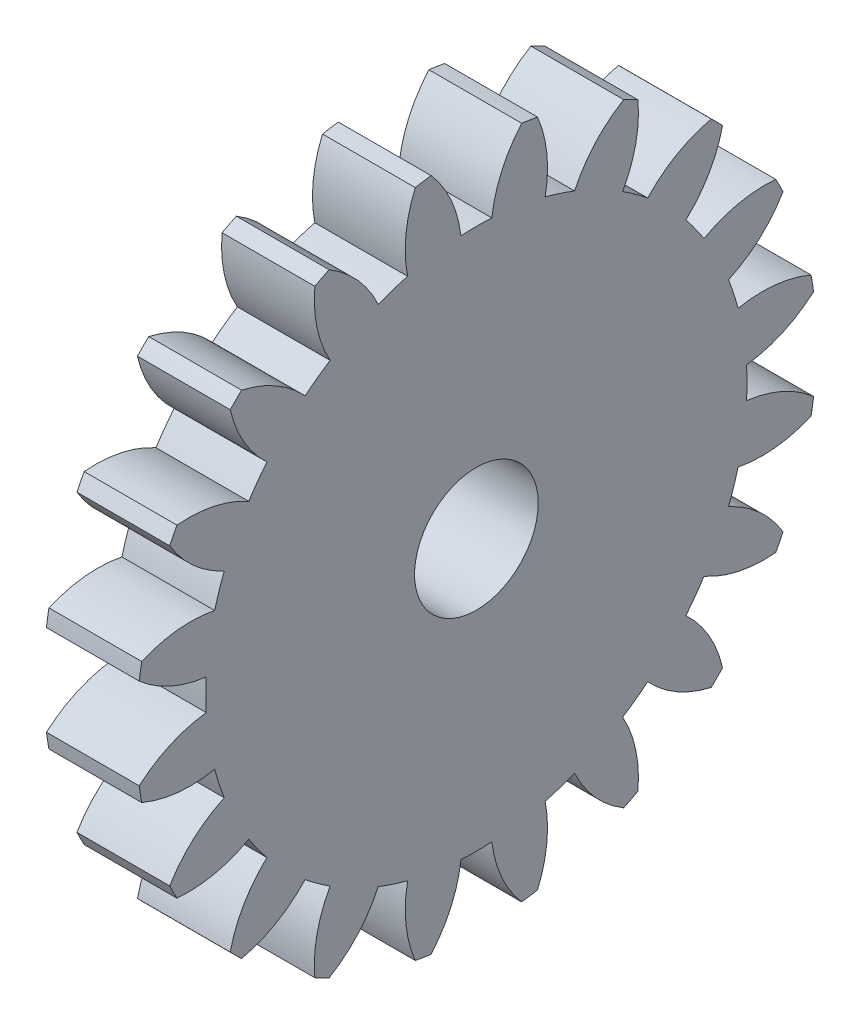
SolidWorks part; units mm, degrees
ref_plane "Plane1" through (0, 0, 0) normal (0, 0, 1) x (1, 0, 0)
ref_plane "Plane2" through (0, 0, 0) normal (0, 1, 0) x (1, 0, 0)
ref_plane "Plane3" through (0, 0, 0) normal (1, 0, 0) x (0, 0, -1)
sketch "HoldingSke" plane through (0, 0, 0) normal (0, 1, 0) x (1, 0, 0)
  line L0 (0, 0) -> (0.9397, -0.342)
  line L1 (-15, 0) -> (100, 0) construction
  line L2 (0, 0) -> (-2.1039, 2.3779)
  line L3 (0, 0) -> (-11.863, 4.5341)
  line L4 (0, 0) -> (8.1152, 2.9537)
  line L5 (0, 0) -> (-46.8476, -17.4728)
  line L6 (0, 0) -> (-2.4869, -1.6779)
  line L7 (-2.1039, 2.3779) -> (8.6586, 51.2059)
  line L8 (-76.2, 54.61) -> (-75.7, 54.61)
  line L9 (-71.009, 38.7566) -> (-53.1078, 45.2721)
  line L10 (-76.2, 71.12) -> (104.1128, 71.12)
  line L11 (0, 0) -> (-3, 0)
  line L12 (-76.2, 101.6) -> (-76.162, 101.6)
  line L13 (24.9733, 27.94) -> (52.9518, 28.4284)
  line L14 (24.9733, 27.94) -> (24.9743, 27.94)
  line L15 (24.9733, 27.94) -> (100.4006, 29.5858)
  line L16 (-63.627, -1) -> (-12.827, -1)
  circle A0 centre (0, 0) radius 1.5
  circle A1 centre (0, 0) radius 8.749
  circle A2 centre (0, 0) radius 37.5
  circle A3 centre (0, 0) radius 1.5
  dimension "MHD" = 17.498
  dimension "Hub_dia" = 75
  dimension "Bore" = 3
  dimension "MBD" = 3
  dimension "Num_teeth" = 20
  dimension "Pitch" = 1
  dimension "Overall_len" = 50
  dimension "Show_teeth" = 20
  dimension "Thickness" = 3
  dimension "OAL" = 50.0001
  dimension "T_dim" = 0.5
  dimension "Ap" = 20
  dimension "H" = 19.05
  dimension "Pitch_radius" = 180.3128
  dimension "Width" = 3
  dimension "Backlash" = 0.038
  dimension "Addendum_fac" = 1
  dimension "Dedendum_fac" = 1.25
  dimension "Clearance_fac" = 0.25
  dimension "Dedendum_add" = 0.001
  dimension "Module" = 1
sketch "BasProSke" plane through (0, 0, 0) normal (0, 1, 0) x (1, 0, 0)
  line L0 (-10, 0) -> (60, 0) construction
  line L1 (0, 0) -> (0, 11)
  line L2 (0, 0) -> (3, 0)
  line L3 (3, 0) -> (3, 11)
  line L4 (3, 11) -> (0, 11)
  dimension "Thickness" = 3
  dimension "Diameter" = 22
revolve "Base-Revolve" add sketch "BasProSke" angle 360 about L0
sketch "TooCutSke" plane through (0, 0, 0) normal (1, 0, 0) x (0, 0, -1)
  line L1 (0, 0) -> (0, 107) construction
  line L2 (0, 0) -> (-0.8511, 9.9637) construction
  line L3 (0, 0) -> (-3.1206, 19.7028) construction
  line L4 (-0.8511, 9.9637) -> (-1.5603, 9.8514) construction
  arc A0 (0.4999, 8.7347) -> (-0.4999, 8.7347) centre (0, 0) ccw
  arc A1 (1.4852, 10.9249) -> (-1.4852, 10.9249) centre (0, 0) ccw
  circle A2 centre (0, 0) radius 10 construction
  circle A3 centre (0, 0) radius 9.3969 construction
  arc A4 (-0.4999, 8.7347) -> (-1.4852, 10.9249) centre (-4.4722, 8.2645) ccw
  arc A5 (1.4852, 10.9249) -> (0.4999, 8.7347) centre (4.4722, 8.2645) ccw
  dimension "Root_dia" = 17.498
  dimension "Overcut_dia" = 22.0508
  dimension "Pitch_dia" = 20
  dimension "Base_dia" = 18.7939
  dimension "Flank_rad" = 4
  dimension "Half_ang" = 9
  dimension "Half_CT" = 0.7181
extrude "ToothCut" cut sketch "TooCutSke" along normal through all
fillet "Breaks" [suppressed] radius 0.02
fillet "RootFillets" [suppressed] radius 0.251
pattern_circular "TeethCuts" count 20 every 18 about axis through (-10, 0, 0) along (1, 0, 0) of "ToothCut", "RootFillets", "Breaks"
sketch "HubNeaOneSke" plane through (0, 0, 0) normal (-1, 0, 0) x (0, 0, 1)
  circle A0 centre (0, 0) radius 8.749
  dimension "Diameter" = 17.498
extrude "HubNearOne" [suppressed] add sketch "HubNeaOneSke" along normal blind 47.0001
sketch "HubNeaBotSke" plane through (0, 0, 0) normal (-1, 0, 0) x (0, 0, 1)
  circle A0 centre (0, 0) radius 8.749
  dimension "Diameter" = 17.498
extrude "HubNearBoth" [suppressed] add sketch "HubNeaBotSke" along normal blind 23.5
ref_plane "FarPln" through (3, 0, 0) normal (1, 0, 0) x (0, 0, -1)
sketch "HubFarSke" plane through (3, 0, 0) normal (1, 0, 0) x (0, 0, -1)
  circle A0 centre (0, 0) radius 8.749
  dimension "Diameter" = 17.498
extrude "HubFar" [suppressed] add sketch "HubFarSke" along normal blind 23.5
sketch "BorSke" plane through (0, 0, 0) normal (1, 0, 0) x (0, 0, -1)
  circle A0 centre (0, 0) radius 1.5
  dimension "Diameter" = 3
extrude "Bore" cut sketch "BorSke" along normal mid plane 100.0001
sketch "KeySke" plane through (0, 0, 0) normal (1, 0, 0) x (0, 0, -1)
  line L0 (-0.6, 0) -> (-0.6, 2)
  line L1 (-0.6, 2) -> (0.6, 2)
  line L2 (0.6, 2) -> (0.6, 0)
  line L3 (0, 0) -> (0, 34) construction
  line L4 (-0.6, 0) -> (0.6, 0)
  dimension "Offset" = 2
  dimension "Width" = 1.2
extrude "Keyway" [suppressed] cut sketch "KeySke" along normal mid plane 100.0001
pattern_circular "Keyway2" [suppressed] count 2 every 90 about axis through (-10, 0, 0) along (1, 0, 0)
sketch "Sketch1" plane through (3, 0, 0) normal (1, 0, 0) x (0, 0, -1)
  circle A0 centre (0, 0) radius 2
  dimension "D1" = 4
extrude "Cut-Extrude1" cut sketch "Sketch1" against normal through all
equation "' \"Module@HoldingSke\" = 6.35"
equation "' \"Num_teeth@HoldingSke\" = 12"
equation "' \"Ap@HoldingSke\" =  20"
equation "' \"Ap@HoldingSke\" = 20"
equation "' \"Width@HoldingSke\" = 0.5 * 25.4"
equation "' \"Hub_dia@HoldingSke\"= 1 * 25.4"
equation "' \"Hub_dia@HoldingSke\" = 1 * 25.4"
equation "' \"Overall_len@HoldingSke\" = 1.0 * 25.4"
equation "' \"Bore@HoldingSke\" = 0.75 * 25.4"
equation "' \"T_dim@HoldingSke\" = 0.1 * 25.4"
equation "' \"Width@KeySke\" = 0.25 * 25.4"
equation "' \"Show_teeth@HoldingSke\" = 13"
equation "' \"Backlash@HoldingSke\" = 0.009 * 25.4"
equation "' \"Addendum_fac@HoldingSke\" = 1.0"
equation "' \"Dedendum_fac@HoldingSke\" = 1.25"
equation "' \"Dedendum_add@HoldingSke\" = 0.00005 * 25.4"
equation "' \"Clearance_fac@HoldingSke\" = 0.25"
equation "\"Pitch@HoldingSke\" = 1 / \"Module@HoldingSke\""
equation "\"Overcut_dia@TooCutSke\" = (\"Num_teeth@HoldingSke\" + 2 * \"Addendum_fac@HoldingSke\") / \"Pitch@HoldingSke\" + 0.002 * 25.4"
equation "\"Pitch_dia@TooCutSke\" = \"Num_teeth@HoldingSke\" / \"Pitch@HoldingSke\""
equation "\"Base_dia@TooCutSke\" = \"Num_teeth@HoldingSke\" / \"Pitch@HoldingSke\" * cos((\"Ap@HoldingSke\"  * 3.14159265 / 180))"
equation "\"Root_dia@TooCutSke\" = (\"Num_teeth@HoldingSke\" + 2) / \"Pitch@HoldingSke\" - 2 * (\"Addendum_fac@HoldingSke\" + \"Dedendum_fac@HoldingSke\") / \"Pitch@HoldingSke\" - \"Dedendum_add@HoldingSke\" * 2"
equation "\"Half_ang@TooCutSke\" = 180 / \"Num_teeth@HoldingSke\""
equation "\"Half_CT@TooCutSke\" = \"Num_teeth@HoldingSke\" / \"Pitch@HoldingSke\" * sin((3.14159265 / 2 / \"Num_teeth@HoldingSke\")) / 2 - 7 * \"Backlash@HoldingSke\" / 4"
equation "\"Flank_rad@TooCutSke\" = \"Num_teeth@HoldingSke\" / \"Pitch@HoldingSke\" / 5"
equation "\"Radius@RootFillets\" = \"Clearance_fac@HoldingSke\" / \"Pitch@HoldingSke\" + \"Dedendum_add@HoldingSke\""
equation "\"Break_rad@Breaks\" = 0.02 / \"Pitch@HoldingSke\""
equation "\"Thickness@HoldingSke\" = \"Width@HoldingSke\""
equation "\"OAL@HoldingSke\" = \"Thickness@HoldingSke\""
equation "\"MHD@HoldingSke\" = (\"Num_teeth@HoldingSke\" + 2) / \"Pitch@HoldingSke\" - 2 * (\"Addendum_fac@HoldingSke\" + \"Dedendum_fac@HoldingSke\")  / \"Pitch@HoldingSke\" - \"Dedendum_add@HoldingSke\" * 2"
equation "\"MBD@HoldingSke\" = (\"Num_teeth@HoldingSke\" + 2) / \"Pitch@HoldingSke\" - 2 * (\"Addendum_fac@HoldingSke\" + \"Dedendum_fac@HoldingSke\")  / \"Pitch@HoldingSke\" - \"Dedendum_add@HoldingSke\" * 2 - 0.002 * 25.4"
equation "\"MHD@HoldingSke\" = ((sgn( \"MHD@HoldingSke\" - \"Hub_dia@HoldingSke\" )-1)*( \"MHD@HoldingSke\" - \"Hub_dia@HoldingSke\" ))/-2+ \"Hub_dia@HoldingSke\""
equation "\"MBD@HoldingSke\" = ((sgn( \"MBD@HoldingSke\" - \"Bore@HoldingSke\" )-1)*( \"MBD@HoldingSke\" - \"Bore@HoldingSke\" ))/-2+ \"Bore@HoldingSke\""
equation "\"OAL@HoldingSke\" = ((sgn( \"OAL@HoldingSke\" - \"Overall_len@HoldingSke\" )+1)*( \"OAL@HoldingSke\" - \"Overall_len@HoldingSke\" ))/2 + \"Overall_len@HoldingSke\" + 0.000002 * 25.4"
equation "\"Num_teeth@TeethCuts\" = int( \"Show_teeth@HoldingSke\" ) + 1"
equation "\"Num_teeth@TeethCuts\" = ((sgn( \"Num_teeth@TeethCuts\" - \"Num_teeth@HoldingSke\" )-1)*( \"Num_teeth@TeethCuts\" - \"Num_teeth@HoldingSke\" ))/-2+ \"Num_teeth@HoldingSke\""
equation "\"Num_teeth@TeethCuts\" = ((sgn( \"Num_teeth@TeethCuts\" - 2.0)+1)*( \"Num_teeth@TeethCuts\" - 2.0))/2 +2.0"
equation "\"Angle@TeethCuts\" = 360.0 / \"Num_teeth@HoldingSke\""
equation "\"Diameter@BasProSke\" = (\"Num_teeth@HoldingSke\" + 2 * \"Addendum_fac@HoldingSke\") / \"Pitch@HoldingSke\""
equation "\"Thickness@BasProSke\"  = \"Thickness@HoldingSke\""
equation "' \"Fillet_rad@BasProSke\" =  \"Thickness@HoldingSke\" * 0.05"
equation "' \"Fillet_rad@BasProSke\" = \"Thickness@HoldingSke\" * 0.05"
equation "\"MHD@HoldingSke\" = ((sgn( \"MHD@HoldingSke\" - \"Root_dia@TooCutSke\" )-1)*( \"MHD@HoldingSke\" - \"Root_dia@TooCutSke\" ))/-2+ \"Root_dia@TooCutSke\""
equation "\"Diameter@HubNeaOneSke\" = \"MHD@HoldingSke\""
equation "\"Length@HubNearOne\" = \"OAL@HoldingSke\" - \"Thickness@BasProSke\""
equation "\"Diameter@HubNeaBotSke\" = \"MHD@HoldingSke\""
equation "\"Length@HubNearBoth\" = ( \"OAL@HoldingSke\" - \"Thickness@BasProSke\" ) / 2.0"
equation "\"Thickness@FarPln\" = \"Thickness@BasProSke\""
equation "\"Diameter@HubFarSke\" = \"MHD@HoldingSke\""
equation "\"Length@HubFar\" = ( \"OAL@HoldingSke\" - \"Thickness@BasProSke\" ) / 2.0"
equation "\"Diameter@BorSke\" = \"MBD@HoldingSke\""
equation "\"D1@Bore\" = \"OAL@HoldingSke\" * 2.0"
equation "\"D1@Keyway\" = \"OAL@HoldingSke\" * 2.0"
equation "\"Offset@KeySke\" = \"T_dim@HoldingSke\" + \"MBD@HoldingSke\" / 2.0"
